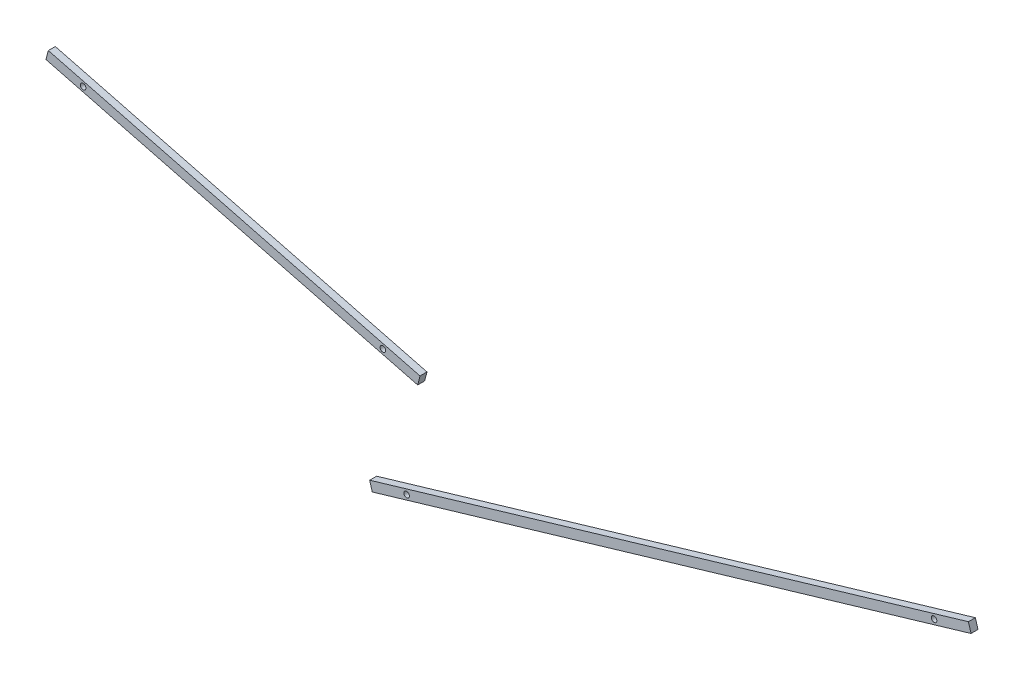
SolidWorks part; units mm, degrees
ref_plane "Front Plane" through (0, 0, 0) normal (0, 0, 1) x (1, 0, 0)
ref_plane "Top Plane" through (0, 0, 0) normal (0, 1, 0) x (1, 0, 0)
ref_plane "Right Plane" through (0, 0, 0) normal (1, 0, 0) x (0, 0, -1)
sketch "Sketch1" plane through (0, 0, 0) normal (0, 0, 1) x (1, 0, 0)
  line L1 (0, 0) -> (914.4, 0) construction
  line L2 (0, 0) -> (0, 609.6) construction
  line L3 (0, 609.6) -> (914.4, 609.6) construction
  line L4 (914.4, 0) -> (914.4, 609.6) construction
  point P0 (0, 0)
  point P6 (0, 0)
  dimension "D1" = 609.6
  dimension "D2" = 914.4
sketch "Sketch4" plane through (0, 0, 0) normal (0, 0, 1) x (1, 0, 0)
  line L1 (420.3734, 450.1336) -> (166.3082, 515.7472)
  line L2 (420.3734, 450.1336) -> (418.7856, 443.9853)
  line L3 (418.7856, 443.9853) -> (164.7203, 509.5989)
  line L4 (166.3082, 515.7472) -> (164.7203, 509.5989)
  line L5 (795.2242, 492.0843) -> (385.9658, 371.2211)
  line L6 (795.2242, 492.0843) -> (797.0227, 485.9943)
  line L7 (797.0227, 485.9943) -> (387.7643, 365.1311)
  line L8 (385.9658, 371.2211) -> (387.7643, 365.1311)
  point P8 (811.0147, 457.6995)
  point P9 (548.0493, 343.2848)
  point P10 (420.3734, 443.9853)
  point P11 (387.7643, 371.2211)
  dimension "D1" = 6.35
  dimension "D2" = 90
  dimension "D3" = 6.35
  dimension "D4" = 90
extrude "Boss-Extrude1" add sketch "Sketch4" along normal blind 4.7625
hole_wizard "#6 Clearance Hole1" positions "Sketch5" profile "Sketch6" hole size "#6" standard "ANSI Inch" end condition through all
sketch "Sketch5" plane through (0, 0, 4.7625) normal (0, 0, 1) x (1, 0, 0)
  line L0 (165.5142, 512.673) -> (419.5795, 447.0595) construction
  line L1 (166.3082, 515.7472) -> (164.7203, 509.5989) construction
  line L2 (418.7856, 443.9853) -> (420.3734, 450.1336) construction
  line L3 (386.8651, 368.1761) -> (796.1235, 489.0393) construction
  line L4 (385.9658, 371.2211) -> (387.7643, 365.1311) construction
  line L5 (797.0227, 485.9943) -> (795.2242, 492.0843) construction
  point P14 (394.9864, 453.4107)
  point P16 (190.1074, 506.3218)
  point P18 (411.225, 375.3701)
  point P20 (771.7636, 481.8452)
  dimension "D1" = 25.4
  dimension "D2" = 25.4
  dimension "D3" = 25.4
  dimension "D4" = 25.4
sketch "Sketch6" plane through (771.7636, 481.8452, 4.7625) normal (1, 0, 0) x (0, -1, 0)
  line L0 (0, 0) -> (0, 4.7625)
  line L1 (0, 4.7625) -> (1.8986, 4.7625)
  line L2 (1.8986, 4.7625) -> (1.8986, 0)
  line L5 (1.8986, 0) -> (0, 0)
  line L11 (0, -6.35) -> (0, 107.95) construction
  dimension "Thru Hole Dia." = 3.7973
  dimension "Thru Hole Depth" = 4.7625
equation "\"holeDistance\"=1"
equation "\"D1@Sketch5\"=\"holeDistance\""
equation "\"D2@Sketch5\"=\"holeDistance\""
equation "\"D3@Sketch5\"=\"holeDistance\""
equation "\"D4@Sketch5\"=\"holeDistance\""
